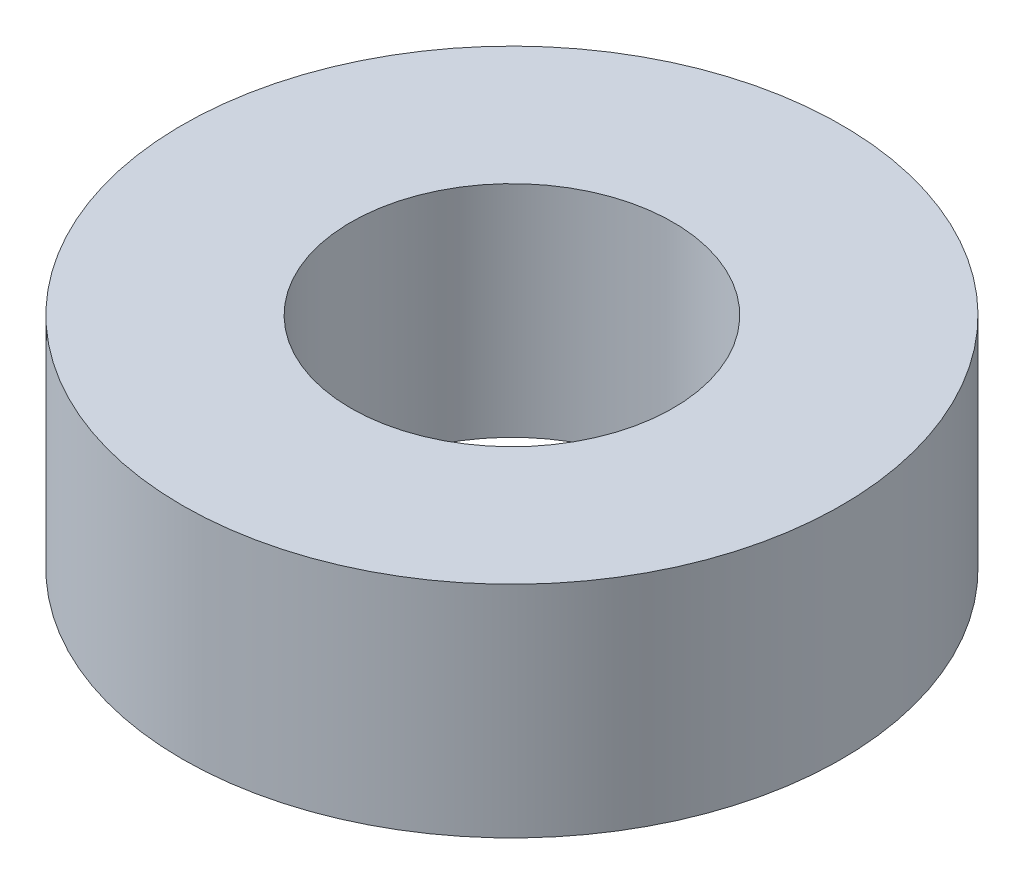
SolidWorks part; units mm, degrees
ref_plane "Front Plane" through (0, 0, 0) normal (0, 0, 1) x (1, 0, 0)
ref_plane "Top Plane" through (0, 0, 0) normal (0, 1, 0) x (1, 0, 0)
ref_plane "Right Plane" through (0, 0, 0) normal (1, 0, 0) x (0, 0, -1)
sketch "Sketch2" plane through (0, 0, 0) normal (0, 1, 0) x (1, 0, 0)
  circle A0 centre (0, 0) radius 2.2
  circle A1 centre (0, 0) radius 4.5
  dimension "D1" = 4.4
  dimension "D2" = 9
extrude "Boss-Extrude1" add sketch "Sketch2" along normal blind 3
